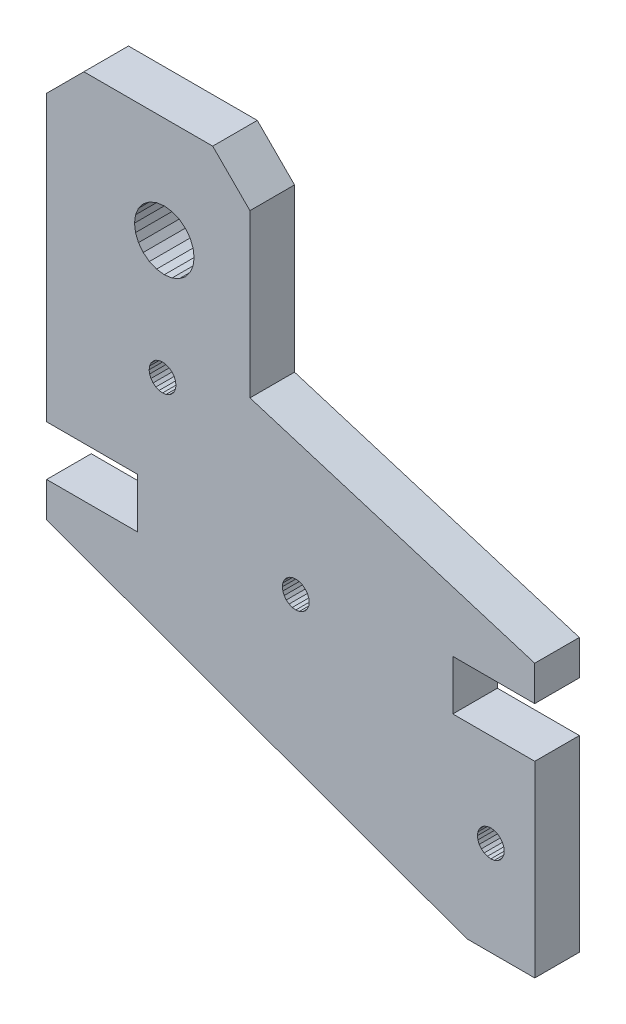
SolidWorks part; units mm, degrees
material "Maple"
ref_plane "Front Plane" through (0, 0, 0) normal (0, 0, 1) x (1, 0, 0)
ref_plane "Top Plane" through (0, 0, 0) normal (0, 1, 0) x (1, 0, 0)
ref_plane "Right Plane" through (0, 0, 0) normal (1, 0, 0) x (0, 0, -1)
sketch "Sketch1" plane through (0, 0, 0) normal (0, 0, 1) x (1, 0, 0)
  line L8120 (349.8059, 49.8321) -> (349.8059, 56.5467)
  line L8121 (349.8059, 56.5467) -> (337.583, 56.5467)
  line L8122 (337.583, 45.1213) -> (337.583, 49.8321)
  line L8123 (337.583, 49.8321) -> (349.8059, 49.8321)
  line L8124 (337.583, 56.5467) -> (337.583, 94.8327)
  line L8125 (337.583, 94.8327) -> (342.5942, 99.8439)
  line L8126 (359.9285, 99.8439) -> (342.5942, 99.8439)
  line L8127 (359.9285, 99.8439) -> (364.9398, 94.8327)
  line L8128 (364.9398, 73.0144) -> (364.9398, 94.8327)
  line L8129 (364.9398, 73.0144) -> (403.2545, 61.2575)
  line L8130 (403.2545, 61.2575) -> (403.2545, 56.5467)
  line L8131 (403.2545, 56.5467) -> (392.2321, 56.5467)
  line L8132 (392.2321, 56.5467) -> (392.2321, 49.8321)
  line L8133 (392.2321, 49.8321) -> (403.2613, 49.8321)
  line L8134 (403.2613, 49.8321) -> (403.2613, 24.5809)
  line L8135 (403.2613, 24.5809) -> (394.1408, 24.5809)
  line L8136 (394.1408, 24.5809) -> (337.583, 45.1213)
  line L8137 (396.0724, 38.5851) -> (396.446, 38.8718)
  line L8138 (396.446, 38.8718) -> (396.8811, 39.052)
  line L8139 (396.8811, 39.052) -> (397.348, 39.1135)
  line L8140 (397.348, 39.1135) -> (397.8149, 39.052)
  line L8141 (397.8149, 39.052) -> (398.25, 38.8718)
  line L8142 (398.25, 38.8718) -> (398.6237, 38.5851)
  line L8143 (398.6237, 38.5851) -> (398.9104, 38.2115)
  line L8144 (398.9104, 38.2115) -> (399.0906, 37.7764)
  line L8145 (399.0906, 37.7764) -> (399.1521, 37.3094)
  line L8146 (399.1521, 37.3094) -> (399.0906, 36.8425)
  line L8147 (399.0906, 36.8425) -> (398.9104, 36.4074)
  line L8148 (398.9104, 36.4074) -> (398.6237, 36.0338)
  line L8149 (398.6237, 36.0338) -> (398.25, 35.7471)
  line L8150 (398.25, 35.7471) -> (397.8149, 35.5669)
  line L8151 (397.8149, 35.5669) -> (397.348, 35.5054)
  line L8152 (397.348, 35.5054) -> (396.8811, 35.5669)
  line L8153 (396.8811, 35.5669) -> (396.446, 35.7471)
  line L8154 (396.446, 35.7471) -> (396.0724, 36.0338)
  line L8155 (396.0724, 36.0338) -> (395.7857, 36.4074)
  line L8156 (395.7857, 36.4074) -> (395.6054, 36.8425)
  line L8157 (395.6054, 36.8425) -> (395.544, 37.3094)
  line L8158 (395.544, 37.3094) -> (395.6054, 37.7764)
  line L8159 (395.6054, 37.7764) -> (395.7857, 38.2115)
  line L8160 (395.7857, 38.2115) -> (396.0724, 38.5851)
  line L8161 (351.3754, 69.5141) -> (351.4369, 69.0472)
  line L8162 (351.4369, 69.981) -> (351.3754, 69.5141)
  line L8163 (351.6171, 70.4161) -> (351.4369, 69.981)
  line L8164 (351.9038, 70.7897) -> (351.6171, 70.4161)
  line L8165 (352.2774, 71.0764) -> (351.9038, 70.7897)
  line L8166 (352.7125, 71.2567) -> (352.2774, 71.0764)
  line L8167 (353.1794, 71.3181) -> (352.7125, 71.2567)
  line L8168 (353.6464, 71.2567) -> (353.1794, 71.3181)
  line L8169 (354.0815, 71.0764) -> (353.6464, 71.2567)
  line L8170 (354.4551, 70.7897) -> (354.0815, 71.0764)
  line L8171 (354.7418, 70.4161) -> (354.4551, 70.7897)
  line L8172 (354.922, 69.981) -> (354.7418, 70.4161)
  line L8173 (354.9835, 69.5141) -> (354.922, 69.981)
  line L8174 (354.922, 69.0472) -> (354.9835, 69.5141)
  line L8175 (354.7418, 68.6121) -> (354.922, 69.0472)
  line L8176 (354.4551, 68.2384) -> (354.7418, 68.6121)
  line L8177 (354.0815, 67.9517) -> (354.4551, 68.2384)
  line L8178 (353.6464, 67.7715) -> (354.0815, 67.9517)
  line L8179 (353.1794, 67.71) -> (353.6464, 67.7715)
  line L8180 (352.7125, 67.7715) -> (353.1794, 67.71)
  line L8181 (352.2774, 67.9517) -> (352.7125, 67.7715)
  line L8182 (351.9038, 68.2384) -> (352.2774, 67.9517)
  line L8183 (351.6171, 68.6121) -> (351.9038, 68.2384)
  line L8184 (351.4369, 69.0472) -> (351.6171, 68.6121)
  line L8185 (372.3815, 54.465) -> (372.0079, 54.7517)
  line L8186 (372.6682, 54.0914) -> (372.3815, 54.465)
  line L8187 (372.8484, 53.6563) -> (372.6682, 54.0914)
  line L8188 (372.9099, 53.1894) -> (372.8484, 53.6563)
  line L8189 (372.8484, 52.7225) -> (372.9099, 53.1894)
  line L8190 (372.6682, 52.2874) -> (372.8484, 52.7225)
  line L8191 (372.3815, 51.9137) -> (372.6682, 52.2874)
  line L8192 (372.0079, 51.627) -> (372.3815, 51.9137)
  line L8193 (371.5728, 51.4468) -> (372.0079, 51.627)
  line L8194 (371.1059, 51.3853) -> (371.5728, 51.4468)
  line L8195 (370.6389, 51.4468) -> (371.1059, 51.3853)
  line L8196 (370.2038, 51.627) -> (370.6389, 51.4468)
  line L8197 (369.8302, 51.9137) -> (370.2038, 51.627)
  line L8198 (369.5435, 52.2874) -> (369.8302, 51.9137)
  line L8199 (369.3633, 52.7225) -> (369.5435, 52.2874)
  line L8200 (369.3018, 53.1894) -> (369.3633, 52.7225)
  line L8201 (369.3633, 53.6563) -> (369.3018, 53.1894)
  line L8202 (369.5435, 54.0914) -> (369.3633, 53.6563)
  line L8203 (369.8302, 54.465) -> (369.5435, 54.0914)
  line L8204 (370.2038, 54.7517) -> (369.8302, 54.465)
  line L8205 (370.6389, 54.9319) -> (370.2038, 54.7517)
  line L8206 (371.1059, 54.9934) -> (370.6389, 54.9319)
  line L8207 (371.5728, 54.9319) -> (371.1059, 54.9934)
  line L8208 (372.0079, 54.7517) -> (371.5728, 54.9319)
  line L8209 (350.5792, 82.7772) -> (351.4094, 82.1401)
  line L8210 (349.9421, 83.6075) -> (350.5792, 82.7772)
  line L8211 (349.5416, 84.5744) -> (349.9421, 83.6075)
  line L8212 (349.405, 85.612) -> (349.5416, 84.5744)
  line L8213 (349.5416, 86.6496) -> (349.405, 85.612)
  line L8214 (349.9421, 87.6165) -> (349.5416, 86.6496)
  line L8215 (350.5792, 88.4468) -> (349.9421, 87.6165)
  line L8216 (351.4094, 89.0839) -> (350.5792, 88.4468)
  line L8217 (352.3763, 89.4844) -> (351.4094, 89.0839)
  line L8218 (353.4139, 89.621) -> (352.3763, 89.4844)
  line L8219 (354.4515, 89.4844) -> (353.4139, 89.621)
  line L8220 (355.4184, 89.0839) -> (354.4515, 89.4844)
  line L8221 (356.2487, 88.4468) -> (355.4184, 89.0839)
  line L8222 (356.8858, 87.6165) -> (356.2487, 88.4468)
  line L8223 (357.2863, 86.6496) -> (356.8858, 87.6165)
  line L8224 (357.4229, 85.612) -> (357.2863, 86.6496)
  line L8225 (357.2863, 84.5744) -> (357.4229, 85.612)
  line L8226 (356.8858, 83.6075) -> (357.2863, 84.5744)
  line L8227 (356.2487, 82.7772) -> (356.8858, 83.6075)
  line L8228 (355.4184, 82.1401) -> (356.2487, 82.7772)
  line L8229 (354.4515, 81.7396) -> (355.4184, 82.1401)
  line L8230 (353.4139, 81.603) -> (354.4515, 81.7396)
  line L8231 (352.3763, 81.7396) -> (353.4139, 81.603)
  line L8232 (351.4094, 82.1401) -> (352.3763, 81.7396)
  line L9778 (383.0168, 55.1804) -> (383.0168, 50.8664)
  line L9779 (382.0168, 55.1804) -> (383.0168, 55.1804)
  line L9780 (383.0168, 55.1804) -> (384.0168, 55.1804)
  line L9781 (383.0168, 50.8664) -> (382.0168, 50.8664)
  line L9782 (383.0168, 50.8664) -> (384.0168, 50.8664)
extrude "Boss-Extrude1" add sketch "Sketch1" along normal blind 6
